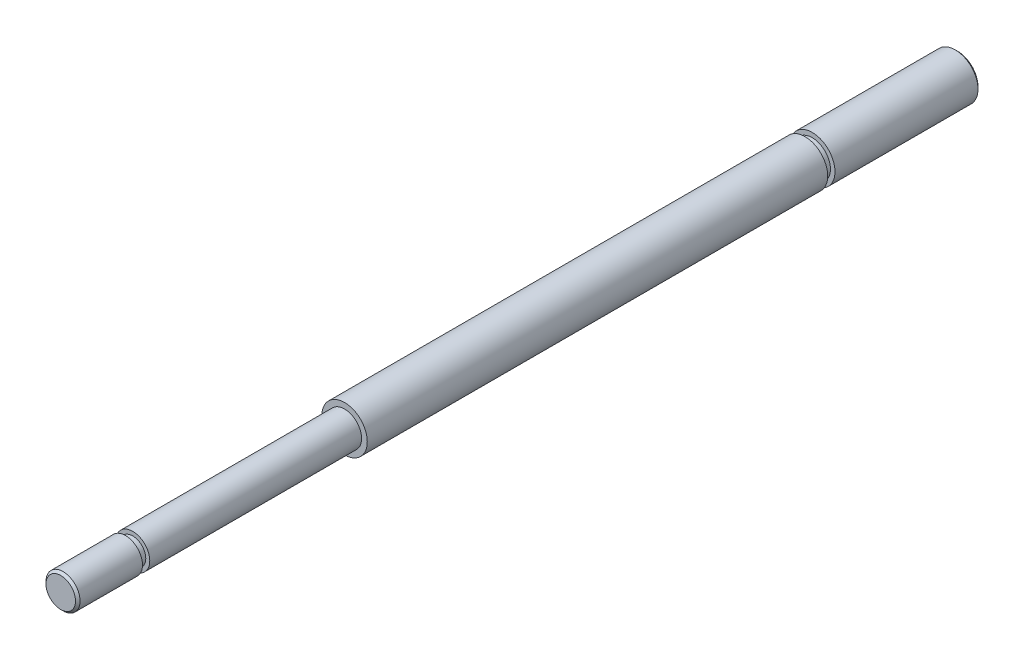
SolidWorks part; units mm, degrees
ref_plane "Plan1" through (0, 0, 0) normal (0, 0, 1) x (1, 0, 0)
ref_plane "Plan2" through (0, 0, 0) normal (0, 1, 0) x (1, 0, 0)
ref_plane "Plan3" through (0, 0, 0) normal (1, 0, 0) x (0, 0, -1)
sketch "Esquisse1" plane through (0, 0, 0) normal (0, 0, 1) x (1, 0, 0)
  circle A0 centre (0, 0) radius 2
  dimension "D1" = 4
extrude "Base-Extrusion" add sketch "Esquisse1" along normal blind 54
sketch "Esquisse2" plane through (0, 0, 54) normal (0, 0, 1) x (1, 0, 0)
  circle A0 centre (0, 0) radius 1.5
  dimension "D1" = 3
extrude "Boss.-Extru.1" add sketch "Esquisse2" along normal blind 25
chamfer "Chanfrein1" distance 0.2 angle 45
sketch "Esquisse3" plane through (0, 0, 0) normal (1, 0, 0) x (0, 0, -1)
  line L0 (0, 0) -> (3.899, 0) construction
  line L1 (-54, 0) -> (-0.2, 0) construction
  line L2 (-78.8, -1.5) -> (-78.8, 1.5) construction
  line L3 (-13.44, 4.0035) -> (-12.8, 4.0035)
  line L4 (-13.44, 4.0035) -> (-13.44, 1.6)
  line L5 (-13.44, 1.6) -> (-12.8, 1.6)
  line L6 (-12.8, 4.0035) -> (-12.8, 1.6)
  line L7 (-73.3, 3.884) -> (-72.66, 3.884)
  line L8 (-73.3, 3.884) -> (-73.3, 1.15)
  line L9 (-73.3, 1.15) -> (-72.66, 1.15)
  line L10 (-72.66, 3.884) -> (-72.66, 1.15)
  dimension "D1" = 0.64
  dimension "D2" = 2.3
  dimension "D3" = 5.5
  dimension "D4" = 0.64
  dimension "D5" = 3.2
  dimension "D6" = 60.5
revolve "Enlèvement de matière-Révolution1" cut sketch "Esquisse3" angle 360 about L0
